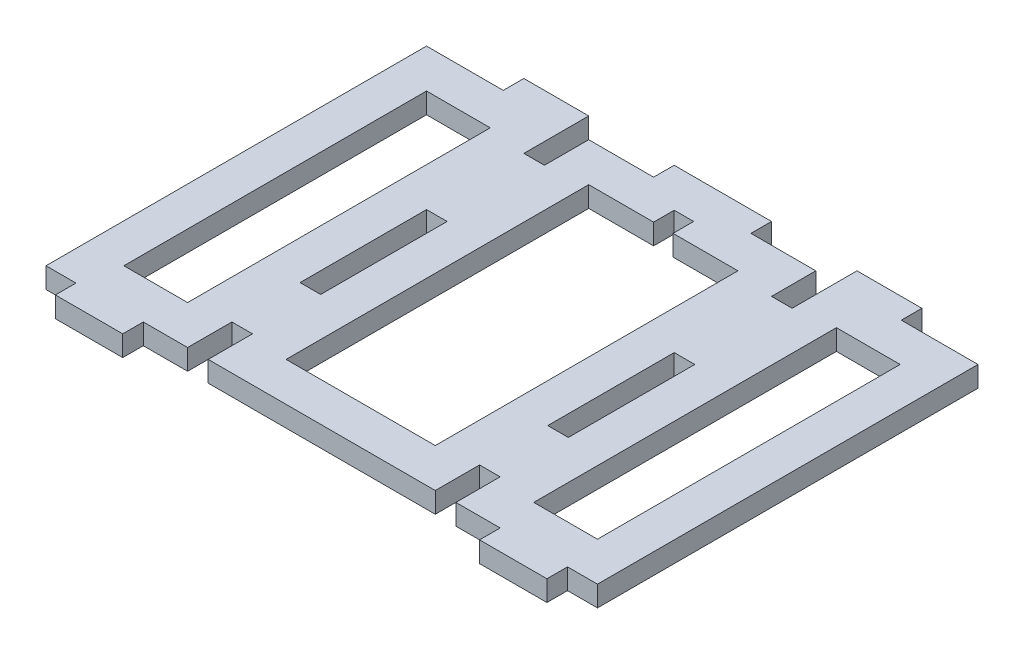
SolidWorks part; units mm, degrees
ref_plane "Front Plane" through (0, 0, 0) normal (0, 0, 1) x (1, 0, 0)
ref_plane "Top Plane" through (0, 0, 0) normal (0, 1, 0) x (1, 0, 0)
ref_plane "Right Plane" through (0, 0, 0) normal (1, 0, 0) x (0, 0, -1)
sketch "Sketch1" plane through (0, 0, 0) normal (0, 1, 0) x (1, 0, 0)
  line L1 (0, 0) -> (85, 0)
  line L2 (0, 0) -> (0, 65)
  line L3 (0, 65) -> (85, 65)
  line L4 (85, 0) -> (85, 65)
  dimension "D1" = 85
  dimension "D2" = 65
extrude "Boss-Extrude1" add sketch "Sketch1" along normal blind 3.175
sketch "Sketch2" plane through (0, 0, 0) normal (0, -1, 0) x (1, 0, 0)
  line L0 (85, -65) -> (0, -65) construction
  line L1 (63.175, -65) -> (60, -65)
  line L2 (63.175, -65) -> (63.175, -55)
  line L3 (63.175, -55) -> (60, -55)
  line L4 (60, -65) -> (60, -55)
  line L5 (63.175, 0) -> (63.175, -10) construction
  line L6 (60, 0) -> (60, -10) construction
  line L7 (21.825, 0) -> (21.825, -10) construction
  line L8 (21.825, -65) -> (25, -65)
  line L9 (21.825, -65) -> (21.825, -55)
  line L10 (21.825, -55) -> (25, -55)
  line L11 (25, -65) -> (25, -55)
  line L12 (25, 0) -> (25, -10) construction
  line L13 (0, 0) -> (85, 0) construction
  line L14 (63.175, 0) -> (60, 0)
  line L15 (63.175, 0) -> (63.175, -10)
  line L16 (63.175, -10) -> (60, -10)
  line L17 (60, 0) -> (60, -10)
  line L18 (0, -65) -> (0, 0) construction
  line L19 (21.825, 0) -> (25, 0)
  line L20 (21.825, 0) -> (21.825, -10)
  line L21 (21.825, -10) -> (25, -10)
  line L22 (25, 0) -> (25, -10)
  line L23 (63.175, -40) -> (60, -40)
  line L24 (63.175, -40) -> (63.175, -20.508)
  line L25 (63.175, -20.508) -> (60, -20.508)
  line L26 (60, -40) -> (60, -20.508)
  line L27 (21.825, -40) -> (25, -40)
  line L28 (21.825, -40) -> (21.825, -20.508)
  line L29 (21.825, -20.508) -> (25, -20.508)
  line L30 (25, -40) -> (25, -20.508)
  line L31 (85, 0) -> (80.381, 0)
  line L32 (85, 0) -> (85, -3.175)
  line L33 (85, -3.175) -> (80.381, -3.175)
  line L34 (80.381, 0) -> (80.381, -3.175)
  line L35 (70, 0) -> (15, 0)
  line L36 (70, 0) -> (70, -3.175)
  line L37 (70, -3.175) -> (15, -3.175)
  line L38 (15, 0) -> (15, -3.175)
  line L39 (4.619, 0) -> (0, 0)
  line L40 (4.619, 0) -> (4.619, -3.175)
  line L41 (4.619, -3.175) -> (0, -3.175)
  line L42 (0, 0) -> (0, -3.175)
  line L44 (70, 0.9283) -> (70, 0) construction
  line L45 (15, 0) -> (15, 0.9283) construction
  line L47 (73.175, -65) -> (73.175, -67.4322) construction
  line L48 (0, -65) -> (11.825, -65)
  line L49 (0, -65) -> (0, -61.825)
  line L50 (0, -61.825) -> (11.825, -61.825)
  line L51 (11.825, -65) -> (11.825, -61.825)
  line L52 (25, -65) -> (35, -65)
  line L53 (25, -65) -> (25, -61.825)
  line L54 (25, -61.825) -> (35, -61.825)
  line L55 (35, -65) -> (35, -61.825)
  line L56 (50, -65) -> (60, -65)
  line L57 (50, -65) -> (50, -61.825)
  line L58 (50, -61.825) -> (60, -61.825)
  line L59 (60, -65) -> (60, -61.825)
  line L60 (85, -65) -> (73.175, -65)
  line L61 (85, -65) -> (85, -61.825)
  line L62 (85, -61.825) -> (73.175, -61.825)
  line L63 (73.175, -65) -> (73.175, -61.825)
  line L64 (50, -65) -> (50, -67.4322) construction
  line L65 (35, -65) -> (35, -67.4322) construction
  line L66 (11.825, -65) -> (11.825, -67.4322) construction
  line M11 (0, 0) -> (0, -65)
  line M12 (0, -65) -> (85, -65)
  line M13 (85, -65) -> (85, 0)
  line M14 (85, 0) -> (0, 0)
  dimension "D1" = 10
  dimension "D2" = 15
  dimension "D3" = 19.492
  dimension "D4" = 10
  dimension "D5" = 3.175
  dimension "D6" = 3.175
  dimension "D7" = 4.619
  dimension "D8" = 4.619
extrude "Cut-Extrude1" cut sketch "Sketch2" against normal through all contours L22 L37 L20 L21 | L37 L22 L20 M14 | L38 L37 L20 M14 | L41 L40 M14 M11 | L37 L36 L15 M14 | L37 L15 L17 M14 | L34 L33 M14 M13 | L37 L17 L22 M14 | L15 L37 L17 L16 | L26 L23 L24 L25 | L27 L30 L29 L28 | L11 L10 L9 M12 | L4 L2 L3 M12 | L63 L62 M12 M13 | L58 L57 L4 M12 | L55 L54 L11 M12 | L51 L50 M12 M11
sketch "Sketch3" plane through (0, 3.175, 0) normal (0, 1, 0) x (1, 0, 0)
  line L72 (15.825, 55.825) -> (15.825, 7.6338)
  line L73 (31, 55.825) -> (31, 9.175)
  line L74 (54, 55.825) -> (54, 9.175)
  line L75 (69.175, 55.825) -> (69.175, 7.6338)
  line L108 (69.175, 9.175) -> (79, 9.175)
  line L109 (79, 9.175) -> (79, 55.825)
  line L110 (79, 55.825) -> (69.175, 55.825)
  line L111 (69.175, 55.825) -> (69.175, 49)
  line L112 (69.175, 49) -> (54, 49)
  line L113 (54, 49) -> (54, 55.825)
  line L114 (54, 55.825) -> (44, 55.825)
  line L115 (44, 55.825) -> (44, 59)
  line L116 (44, 59) -> (41, 59)
  line L117 (41, 59) -> (41, 55.825)
  line L118 (41, 55.825) -> (31, 55.825)
  line L119 (31, 55.825) -> (31, 49)
  line L120 (31, 49) -> (15.825, 49)
  line L121 (15.825, 49) -> (15.825, 55.825)
  line L122 (15.825, 55.825) -> (6, 55.825)
  line L123 (6, 55.825) -> (6, 9.175)
  line L124 (6, 9.175) -> (15.825, 9.175)
  line L125 (15.825, 9.175) -> (15.825, 16)
  line L126 (15.825, 16) -> (31, 16)
  line L127 (31, 16) -> (31, 9.175)
  line L128 (31, 9.175) -> (54, 9.175)
  line L129 (54, 9.175) -> (54, 16)
  line L130 (54, 16) -> (69.175, 16)
  line L131 (69.175, 16) -> (69.175, 9.175)
  line L132 (69.175, 9.175) -> (79, 9.175)
  line L133 (79, 9.175) -> (79, 55.825)
  line L134 (79, 55.825) -> (69.175, 55.825)
  line L138 (54, 55.825) -> (44, 55.825)
  line L139 (44, 55.825) -> (44, 59)
  line L140 (44, 59) -> (41, 59)
  line L141 (41, 59) -> (41, 55.825)
  line L142 (41, 55.825) -> (31, 55.825)
  line L146 (15.825, 55.825) -> (6, 55.825)
  line L147 (6, 55.825) -> (6, 9.175)
  line L148 (6, 9.175) -> (15.825, 9.175)
  line L152 (31, 9.175) -> (54, 9.175)
  dimension "D1" = 6
extrude "Cut-Extrude2" cut sketch "Sketch3" against normal through all
